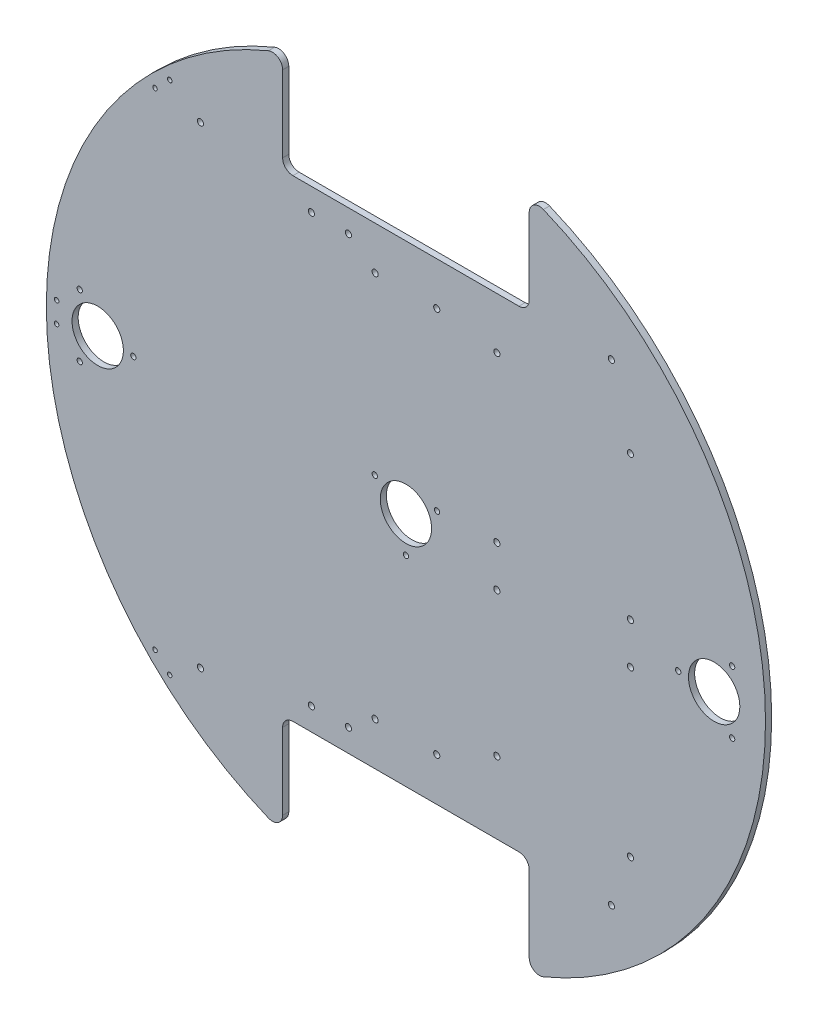
SolidWorks part; units mm, degrees
material "ｱｸﾘﾙ (中-上級の耐衝撃性)"
ref_plane "正面" through (0, 0, 0) normal (0, 0, 1) x (1, 0, 0)
ref_plane "平面" through (0, 0, 0) normal (0, 1, 0) x (1, 0, 0)
ref_plane "右側面" through (0, 0, 0) normal (1, 0, 0) x (0, 0, -1)
sketch "ｽｹｯﾁ1" plane through (0, 0, 0) normal (0, 0, 1) x (1, 0, 0)
  circle A0 centre (0, 0) radius 175
  dimension "D1" = 350
extrude "ﾎﾞｽ - 押し出し1" add sketch "ｽｹｯﾁ1" along normal blind 3
sketch "ｽｹｯﾁ2" plane through (0, 0, 3) normal (0, 0, 1) x (1, 0, 0)
  line L0 (0, 0) -> (175, 0)
  line L1 (0, 0) -> (-175, 0)
  line L2 (0, 0) -> (0, 115)
  line L3 (0, 0) -> (0, -115)
  line L4 (0, 115) -> (60, 115)
  line L5 (0, 115) -> (0, 175)
  line L6 (0, 175) -> (60, 175)
  line L7 (60, 115) -> (60, 175)
  line L8 (0, 115) -> (-60, 115)
  line L9 (0, 115) -> (0, 175)
  line L10 (0, 175) -> (-60, 175)
  line L11 (-60, 115) -> (-60, 175)
  line L13 (0, -115) -> (60, -115)
  line L14 (0, -115) -> (0, -175)
  line L15 (0, -175) -> (60, -175)
  line L16 (60, -115) -> (60, -175)
  line L17 (0, -115) -> (-60, -115)
  line L18 (0, -115) -> (0, -175)
  line L19 (0, -175) -> (-60, -175)
  line L20 (-60, -115) -> (-60, -175)
  circle A0 centre (0, 0) radius 175 construction
  circle M1 centre (0, 0) radius 175
  dimension "D1" = 115
  dimension "D2" = 60
  dimension "D3" = 60
  dimension "D4" = 60
  dimension "D5" = 115
  dimension "D6" = 60
extrude "ｶｯﾄ - 押し出し1" cut sketch "ｽｹｯﾁ2" against normal blind 3 contours L11 L8 L5 M1 | L4 L7 L5 M1 | L17 L20 L14 M1 | L16 L13 L14 M1
fillet "ﾌｨﾚｯﾄ1" radius 5 1 edges at (-60, 164.3928, 1.5)
fillet "ﾌｨﾚｯﾄ2" radius 5 3 edges at (60, 115, 1.5) (60, 164.3928, 1.5) (-60, 115, 1.5)
fillet "ﾌｨﾚｯﾄ3" radius 5 4 edges at (-60, -164.3928, 1.5) (-60, -115, 1.5) (60, -164.3928, 1.5) (60, -115, 1.5)
sketch "ｽｹｯﾁ5" plane through (0, 0, 3) normal (0, 0, 1) x (1, 0, 0)
  line L0 (0, 115) -> (-100, 115)
  line L1 (55, 115) -> (-55, 115) construction
  line L2 (0, 115) -> (100, 115)
  line L3 (0, -115) -> (100, -115)
  line L4 (55, -115) -> (-55, -115) construction
  line L5 (100, -115) -> (-100, -115)
  circle A0 centre (-100, -115) radius 1.5
  circle A1 centre (100, -115) radius 1.5
  circle A2 centre (100, 115) radius 1.5
  circle A3 centre (-100, 115) radius 1.5
  dimension "D3" = 3
  dimension "D4" = 3
  dimension "D5" = 3
  dimension "D6" = 3
  dimension "D1" = 100
  dimension "D2" = 100
extrude "ｶｯﾄ - 押し出し4" cut sketch "ｽｹｯﾁ5" against normal blind 3 contours A1 | A0 | A3 | A2
sketch "ｽｹｯﾁ10" plane through (0, 0, 3) normal (0, 0, 1) x (1, 0, 0)
  line L0 (0, 0) -> (-150, 0)
  line L1 (0, 0) -> (150, 0)
  line L2 (-150, 0) -> (-158.75, 15.1554)
  line L3 (-150, 0) -> (-158.75, -15.1554)
  line L4 (-150, 0) -> (-132.6329, 0)
  line L5 (0, 0) -> (15.1554, 8.75)
  line L6 (0, 0) -> (-15.1554, 8.75)
  line L7 (0, 0) -> (0, -17.5)
  line L8 (150, 0) -> (158.75, 15.1554)
  line L9 (150, 0) -> (132.5, 0)
  line L10 (150, 0) -> (158.75, -15.1554)
  circle A0 centre (-150, 0) radius 12.5
  circle A1 centre (150, 0) radius 12.5
  circle A2 centre (0, 0) radius 12.5
  circle A3 centre (-150, 0) radius 17.5
  circle A4 centre (0, 0) radius 17.5
  circle A5 centre (150, 0) radius 17.5
  circle A6 centre (132.5, 0) radius 1.3
  circle A7 centre (158.75, 15.1554) radius 1.3
  circle A8 centre (158.75, -15.1554) radius 1.3
  circle A9 centre (-15.1554, 8.75) radius 1.3
  circle A10 centre (15.1554, 8.75) radius 1.3
  circle A11 centre (0, -17.5) radius 1.3
  circle A12 centre (-158.75, 15.1554) radius 1.3
  circle A13 centre (-158.75, -15.1554) radius 1.3
  circle A14 centre (-132.6329, 0) radius 1.3
  dimension "D3" = 25
  dimension "D4" = 25
  dimension "D5" = 25
  dimension "D6" = 35
  dimension "D7" = 35
  dimension "D8" = 35
  dimension "D15" = 2.6
  dimension "D16" = 2.6
  dimension "D17" = 2.6
  dimension "D18" = 2.6
  dimension "D19" = 2.6
  dimension "D20" = 2.6
  dimension "D21" = 2.6
  dimension "D22" = 2.6
  dimension "D23" = 2.6
  dimension "D1" = 150
  dimension "D2" = 150
  dimension "D9" = 120
  dimension "D10" = 120
  dimension "D11" = 120
  dimension "D12" = 120
  dimension "D13" = 120
  dimension "D14" = 120
sketch "ｽｹｯﾁ12" plane through (0, 0, 3) normal (0, 0, 1) x (1, 0, 0)
  line L0 (0, 115) -> (0, 94)
  line L1 (55, 115) -> (-55, 115) construction
  line L2 (0, 94) -> (15, 94)
  line L3 (0, 94) -> (-15, 94)
  line L7 (0, -115) -> (0, -94)
  line L8 (55, -115) -> (-55, -115) construction
  line L9 (0, -94) -> (15, -94)
  line L10 (0, -94) -> (-15, -94)
  circle A0 centre (-15, 94) radius 1.5
  circle A1 centre (15, 94) radius 1.5
  circle A6 centre (-15, -94) radius 1.5
  circle A7 centre (15, -94) radius 1.5
  dimension "D5" = 3
  dimension "D6" = 3
  dimension "D7" = 15
  dimension "D13" = 3
  dimension "D14" = 3
  dimension "D1" = 21
  dimension "D2" = 15
  dimension "D3" = 15
  dimension "D4" = 15
  dimension "D9" = 21
sketch "ｽｹｯﾁ13" plane through (0, 0, 3) normal (0, 0, 1) x (1, 0, 0)
  line L0 (0, -115) -> (-25, -115)
  line L1 (55, -115) -> (-55, -115) construction
  line L2 (-25, -115) -> (-25, -104)
  line L3 (-46, 104) -> (-28, 104)
  line L4 (0, 115) -> (-28, 115)
  line L5 (-28, -104) -> (-46, -104)
  line L6 (-28, 104) -> (-27.8272, 103.8289)
  line L7 (0, 115) -> (0, -115)
  line L9 (55, 115) -> (-55, 115) construction
  line L10 (-28, 115) -> (-28, 104)
  line L12 (-28, 104) -> (-46, 104)
  circle A1 centre (-28, -104) radius 1.5
  circle A2 centre (-46, -104) radius 1.5
  circle A4 centre (-46, 104) radius 1.5
  circle A7 centre (-28, 104) radius 1.5
  dimension "D8" = 3
  dimension "D9" = 3
  dimension "D13" = 3
  dimension "D14" = 3
  dimension "D1" = 25
  dimension "D2" = 11
  dimension "D3" = 3
  dimension "D4" = 18
  dimension "D5" = 18
  dimension "D10" = 28
  dimension "D11" = 11
extrude "ｶｯﾄ - 押し出し13" cut sketch "ｽｹｯﾁ10" against normal blind 10 contours A12 | A0 | A13 | A14 | A2 | A9 | A10 | A11 | A6 | A1 | A7 | A8
sketch "ｽｹｯﾁ14" plane through (0, 0, 3) normal (0, 0, 1) x (1, 0, 0)
  line L0 (0, 0) -> (-170, 0)
  line L1 (-170, 0) -> (-170, 5)
  line L2 (-170, 0) -> (-170, -5)
  line L3 (0, 0) -> (-118.5181, 121.8748)
  line L4 (0, 0) -> (-118.5181, -121.8748)
  line L5 (-118.5181, 121.8748) -> (-114.9335, 125.3606)
  line L6 (-118.5181, 121.8748) -> (-122.1026, 118.389)
  line L7 (-118.5181, -121.8748) -> (-122.1026, -118.389)
  line L8 (-118.5181, -121.8748) -> (-114.9335, -125.3606)
  circle A0 centre (-170, 5) radius 1.1
  circle A1 centre (-170, -5) radius 1.1
  circle A2 centre (-114.9335, 125.3606) radius 1.1
  circle A3 centre (-122.1026, 118.389) radius 1.1
  circle A4 centre (-122.1026, -118.389) radius 1.1
  circle A5 centre (-114.9335, -125.3606) radius 1.1
  dimension "D4" = 2.2
  dimension "D5" = 2.2
  dimension "D14" = 2.2
  dimension "D15" = 2.2
  dimension "D16" = 2.2
  dimension "D17" = 2.2
  dimension "D1" = 170
  dimension "D2" = 5
  dimension "D3" = 5
  dimension "D6" = 45.8
  dimension "D7" = 45.8
  dimension "D8" = 170
  dimension "D9" = 170
  dimension "D10" = 5
  dimension "D11" = 5
  dimension "D12" = 5
  dimension "D13" = 5
extrude "ｶｯﾄ - 押し出し14" cut sketch "ｽｹｯﾁ14" against normal blind 10 contours A4 | A5 | A0 | A1 | A2 | A3
extrude "ｶｯﾄ - 押し出し17" cut sketch "ｽｹｯﾁ12" against normal blind 10 contours A6 | A7 | A0 | A1
extrude "ｶｯﾄ - 押し出し18" cut sketch "ｽｹｯﾁ13" against normal blind 5 contours A2 | A1 | A4 | A7
sketch "ｽｹｯﾁ15" plane through (0, 0, 3) normal (0, 0, 1) x (1, 0, 0)
  line L0 (12.5, 0) -> (131.2, 0) construction
  circle A0 centre (0, 0) radius 12.5 construction
  circle A1 centre (132.5, 0) radius 1.3 construction
  circle A2 centre (44.253, 10) radius 1.5
  circle A3 centre (44.253, 90) radius 1.5
  circle A4 centre (109.253, 10) radius 1.5
  circle A5 centre (109.253, 80) radius 1.5
  circle A6 centre (44.253, -10) radius 1.5
  circle A7 centre (109.253, -10) radius 1.5
  circle A8 centre (44.253, -80) radius 1.5
  circle A9 centre (109.253, -90) radius 1.5
  dimension "D1" = 3
  dimension "D2" = 10
  dimension "D3" = 3
  dimension "D4" = 80
  dimension "D5" = 3
  dimension "D6" = 65
  dimension "D7" = 3
  dimension "D8" = 70
  dimension "D10" = 3
  dimension "D11" = 3
  dimension "D12" = 65
  dimension "D13" = 3
  dimension "D14" = 70
  dimension "D15" = 3
  dimension "D16" = 80
  dimension "D9" = 10
extrude "ｶｯﾄ - 押し出し19" cut sketch "ｽｹｯﾁ15" against normal through all
